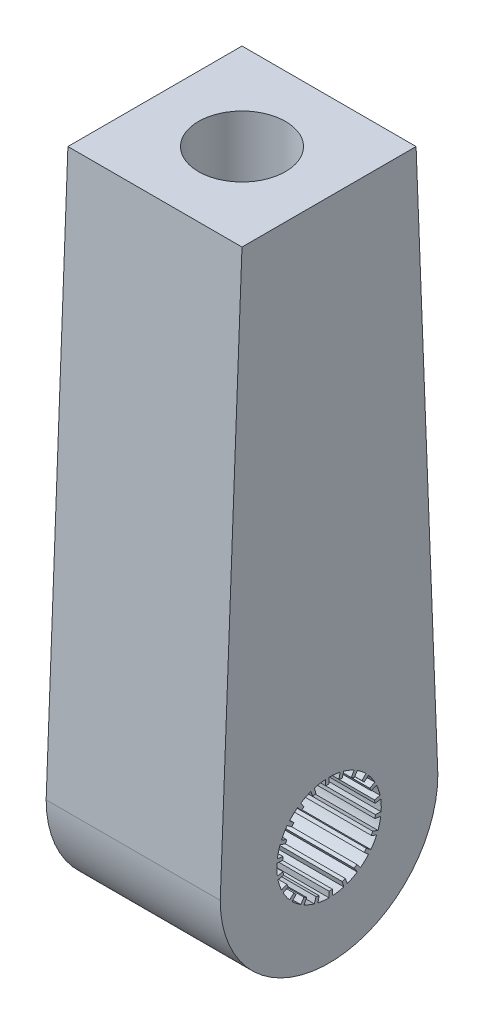
SolidWorks part; units mm, degrees
ref_plane "Front Plane" through (0, 0, 0) normal (0, 0, 1) x (1, 0, 0)
ref_plane "Top Plane" through (0, 0, 0) normal (0, 1, 0) x (1, 0, 0)
ref_plane "Right Plane" through (0, 0, 0) normal (1, 0, 0) x (0, 0, -1)
sketch "Sketch1" plane through (0, 0, 0) normal (1, 0, 0) x (0, 0, -1)
  line L1 (0, 63.75) -> (10, 63.75)
  line L2 (10, 63.75) -> (12.5, 0)
  line L4 (-12.5, 0) -> (-10, 63.75)
  line L5 (-10, 63.75) -> (0, 63.75)
  circle A0 centre (0, 0) radius 6
  arc A2 (-12.4616, 0.9789) -> (12.4616, 0.9789) centre (0, 0) ccw
  dimension "D1" = 12
  dimension "D3" = 25
  dimension "D4" = 63.75
  dimension "D5" = 10
  dimension "D6" = 10
extrude "Boss-Extrude1" add sketch "Sketch1" along normal blind 20 contours A2 A0
sketch "Sketch2" plane through (0, 63.75, 0) normal (0, 1, 0) x (1, 0, 0)
  line L0 (0, -10) -> (0, 10) construction
  circle A0 centre (10, 0) radius 5
  dimension "D2" = 10
  dimension "D1" = 10
extrude "Cut-Extrude1" cut sketch "Sketch2" against normal blind 50
sketch "Sketch3" plane through (20, 0, 0) normal (1, 0, 0) x (0, 0, -1)
  line L0 (-0.0029, 6.4021) -> (-0.0028, 6)
  line L1 (1.5045, 5.1237) -> (1.6904, 5.757)
  line L2 (1.6904, 5.757) -> (1.8037, 6.1428)
  line L3 (2.5593, 4.6868) -> (2.8756, 5.266)
  line L4 (1.1352, 5.2179) -> (1.2755, 5.8629)
  line L5 (2.887, 4.4923) -> (3.2438, 5.0475)
  line L6 (3.2438, 5.0475) -> (3.4612, 5.3858)
  line L7 (1.8009, 6.1436) -> (1.6877, 5.7577)
  line L8 (3.776, 3.7759) -> (4.2427, 4.2426)
  line L9 (4.0357, 3.497) -> (4.5345, 3.9292)
  line L10 (4.5345, 3.9292) -> (4.8384, 4.1925)
  line L11 (3.4588, 5.3874) -> (3.2415, 5.049)
  line L12 (4.6868, 2.5591) -> (5.2661, 2.8754)
  line L13 (4.8574, 2.2183) -> (5.4578, 2.4925)
  line L14 (5.4578, 2.4925) -> (5.8236, 2.6595)
  line L15 (4.8365, 4.1947) -> (4.5327, 3.9313)
  line L16 (5.218, 1.135) -> (5.8629, 1.2753)
  line L17 (5.2856, 0.76) -> (5.9389, 0.8539)
  line L18 (5.9389, 0.8539) -> (6.337, 0.9111)
  line L19 (5.8223, 2.6622) -> (5.4566, 2.495)
  line L20 (5.3264, -0.381) -> (5.9847, -0.4281)
  line L21 (5.2856, -0.76) -> (5.9389, -0.8539)
  line L22 (5.9389, -0.8539) -> (6.337, -0.9111)
  line L23 (6.3365, 0.914) -> (5.9385, 0.8566)
  line L24 (5.0033, -1.8662) -> (5.6217, -2.0969)
  line L25 (4.8574, -2.2183) -> (5.4578, -2.4925)
  line L26 (5.4578, -2.4925) -> (5.8236, -2.6595)
  line L27 (6.3374, -0.9082) -> (5.9393, -0.8512)
  line L28 (4.2748, -3.2002) -> (4.8032, -3.5957)
  line L29 (4.0357, -3.497) -> (4.5345, -3.9292)
  line L30 (4.5345, -3.9292) -> (4.8384, -4.1925)
  line L31 (5.8248, -2.6569) -> (5.4589, -2.49)
  line L32 (3.2001, -4.2749) -> (3.5956, -4.8033)
  line L33 (2.887, -4.4923) -> (3.2438, -5.0475)
  line L34 (3.2438, -5.0475) -> (3.4612, -5.3858)
  line L35 (4.8403, -4.1903) -> (4.5363, -3.9271)
  line L36 (1.8661, -5.0033) -> (2.0967, -5.6217)
  line L37 (1.5045, -5.1237) -> (1.6904, -5.757)
  line L38 (1.6904, -5.757) -> (1.8037, -6.1428)
  line L39 (3.4637, -5.3842) -> (3.2462, -5.046)
  line L40 (0.3809, -5.3264) -> (0.4279, -5.9847)
  line L41 (0, -5.34) -> (0, -6)
  line L42 (0, -6) -> (0, -6.4021)
  line L43 (1.8065, -6.142) -> (1.693, -5.7562)
  line L44 (-1.1352, -5.2179) -> (-1.2755, -5.8629)
  line L45 (-1.5045, -5.1237) -> (-1.6904, -5.757)
  line L46 (-1.6904, -5.757) -> (-1.8037, -6.1428)
  line L47 (0.0029, -6.4021) -> (0.0028, -6)
  line L48 (-2.5593, -4.6868) -> (-2.8756, -5.266)
  line L49 (-2.887, -4.4923) -> (-3.2438, -5.0475)
  line L50 (-3.2438, -5.0475) -> (-3.4612, -5.3858)
  line L51 (-1.8009, -6.1436) -> (-1.6877, -5.7577)
  line L52 (-3.776, -3.7759) -> (-4.2427, -4.2426)
  line L53 (-4.0357, -3.497) -> (-4.5345, -3.9292)
  line L54 (-4.5345, -3.9292) -> (-4.8384, -4.1925)
  line L55 (-3.4588, -5.3874) -> (-3.2415, -5.049)
  line L56 (-4.6868, -2.5591) -> (-5.2661, -2.8754)
  line L57 (-4.8574, -2.2183) -> (-5.4578, -2.4925)
  line L58 (-5.4578, -2.4925) -> (-5.8236, -2.6595)
  line L59 (-4.8365, -4.1947) -> (-4.5327, -3.9313)
  line L60 (-5.218, -1.135) -> (-5.8629, -1.2753)
  line L61 (-5.2856, -0.76) -> (-5.9389, -0.8539)
  line L62 (-5.9389, -0.8539) -> (-6.337, -0.9111)
  line L63 (-5.8223, -2.6622) -> (-5.4566, -2.495)
  line L64 (-5.3264, 0.381) -> (-5.9847, 0.4281)
  line L65 (-5.2856, 0.76) -> (-5.9389, 0.8539)
  line L66 (-5.9389, 0.8539) -> (-6.337, 0.9111)
  line L67 (-6.3365, -0.914) -> (-5.9385, -0.8566)
  line L68 (-5.0033, 1.8662) -> (-5.6217, 2.0969)
  line L69 (-4.8574, 2.2183) -> (-5.4578, 2.4925)
  line L70 (-5.4578, 2.4925) -> (-5.8236, 2.6595)
  line L71 (-6.3374, 0.9082) -> (-5.9393, 0.8512)
  line L72 (-4.2748, 3.2002) -> (-4.8032, 3.5957)
  line L73 (-4.0357, 3.497) -> (-4.5345, 3.9292)
  line L74 (-4.5345, 3.9292) -> (-4.8384, 4.1925)
  line L75 (-5.8248, 2.6569) -> (-5.4589, 2.49)
  line L76 (-3.2001, 4.2749) -> (-3.5956, 4.8033)
  line L77 (-2.887, 4.4923) -> (-3.2438, 5.0475)
  line L78 (-3.2438, 5.0475) -> (-3.4612, 5.3858)
  line L79 (-4.8403, 4.1903) -> (-4.5363, 3.9271)
  line L80 (-1.8661, 5.0033) -> (-2.0967, 5.6217)
  line L81 (-1.5045, 5.1237) -> (-1.6904, 5.757)
  line L82 (-1.6904, 5.757) -> (-1.8037, 6.1428)
  line L83 (-3.4637, 5.3842) -> (-3.2462, 5.046)
  line L84 (-0.3809, 5.3264) -> (-0.4279, 5.9847)
  line L85 (0, 5.34) -> (0, 6)
  line L86 (0, 6) -> (0, 6.4021)
  line L87 (-1.8065, 6.142) -> (-1.693, 5.7562)
  arc A2 (1.3548, 5.8451) -> (1.2755, 5.8629) centre (0, 0) ccw
  arc A3 (1.5045, 5.1237) -> (1.1352, 5.2179) centre (0, 0) ccw
  arc A4 (1.6904, 5.757) -> (1.2755, 5.8629) centre (0, 0) ccw
  arc A6 (-0.0028, 6) -> (1.2755, 5.8629) centre (0, 0) cw
  arc A7 (-0.0029, 6.4021) -> (1.8037, 6.1428) centre (0, 0) cw
  arc A8 (2.887, 4.4923) -> (2.5593, 4.6868) centre (0, 0) ccw
  arc A9 (1.8009, 6.1436) -> (3.4612, 5.3858) centre (0, 0) cw
  arc A10 (1.6877, 5.7577) -> (2.8756, 5.266) centre (0, 0) cw
  arc A11 (4.0357, 3.497) -> (3.776, 3.7759) centre (0, 0) ccw
  arc A12 (3.4588, 5.3874) -> (4.8384, 4.1925) centre (0, 0) cw
  arc A13 (3.2415, 5.049) -> (4.2427, 4.2426) centre (0, 0) cw
  arc A14 (4.8574, 2.2183) -> (4.6868, 2.5591) centre (0, 0) ccw
  arc A15 (4.8365, 4.1947) -> (5.8236, 2.6595) centre (0, 0) cw
  arc A16 (4.5327, 3.9313) -> (5.2661, 2.8754) centre (0, 0) cw
  arc A17 (5.2856, 0.76) -> (5.218, 1.135) centre (0, 0) ccw
  arc A18 (5.8223, 2.6622) -> (6.337, 0.9111) centre (0, 0) cw
  arc A19 (5.4566, 2.495) -> (5.8629, 1.2753) centre (0, 0) cw
  arc A20 (5.2856, -0.76) -> (5.3264, -0.381) centre (0, 0) ccw
  arc A21 (6.3365, 0.914) -> (6.337, -0.9111) centre (0, 0) cw
  arc A22 (5.9385, 0.8566) -> (5.9847, -0.4281) centre (0, 0) cw
  arc A23 (4.8574, -2.2183) -> (5.0033, -1.8662) centre (0, 0) ccw
  arc A24 (6.3374, -0.9082) -> (5.8236, -2.6595) centre (0, 0) cw
  arc A25 (5.9393, -0.8512) -> (5.6217, -2.0969) centre (0, 0) cw
  arc A26 (4.0357, -3.497) -> (4.2748, -3.2002) centre (0, 0) ccw
  arc A27 (5.8248, -2.6569) -> (4.8384, -4.1925) centre (0, 0) cw
  arc A28 (5.4589, -2.49) -> (4.8032, -3.5957) centre (0, 0) cw
  arc A29 (2.887, -4.4923) -> (3.2001, -4.2749) centre (0, 0) ccw
  arc A30 (4.8403, -4.1903) -> (3.4612, -5.3858) centre (0, 0) cw
  arc A31 (4.5363, -3.9271) -> (3.5956, -4.8033) centre (0, 0) cw
  arc A32 (1.5045, -5.1237) -> (1.8661, -5.0033) centre (0, 0) ccw
  arc A33 (3.4637, -5.3842) -> (1.8037, -6.1428) centre (0, 0) cw
  arc A34 (3.2462, -5.046) -> (2.0967, -5.6217) centre (0, 0) cw
  arc A35 (0, -5.34) -> (0.3809, -5.3264) centre (0, 0) ccw
  arc A36 (1.8065, -6.142) -> (0, -6.4021) centre (0, 0) cw
  arc A37 (1.693, -5.7562) -> (0.4279, -5.9847) centre (0, 0) cw
  arc A38 (-1.5045, -5.1237) -> (-1.1352, -5.2179) centre (0, 0) ccw
  arc A39 (0.0029, -6.4021) -> (-1.8037, -6.1428) centre (0, 0) cw
  arc A40 (0.0028, -6) -> (-1.2755, -5.8629) centre (0, 0) cw
  arc A41 (-2.887, -4.4923) -> (-2.5593, -4.6868) centre (0, 0) ccw
  arc A42 (-1.8009, -6.1436) -> (-3.4612, -5.3858) centre (0, 0) cw
  arc A43 (-1.6877, -5.7577) -> (-2.8756, -5.266) centre (0, 0) cw
  arc A44 (-4.0357, -3.497) -> (-3.776, -3.7759) centre (0, 0) ccw
  arc A45 (-3.4588, -5.3874) -> (-4.8384, -4.1925) centre (0, 0) cw
  arc A46 (-3.2415, -5.049) -> (-4.2427, -4.2426) centre (0, 0) cw
  arc A47 (-4.8574, -2.2183) -> (-4.6868, -2.5591) centre (0, 0) ccw
  arc A48 (-4.8365, -4.1947) -> (-5.8236, -2.6595) centre (0, 0) cw
  arc A49 (-4.5327, -3.9313) -> (-5.2661, -2.8754) centre (0, 0) cw
  arc A50 (-5.2856, -0.76) -> (-5.218, -1.135) centre (0, 0) ccw
  arc A51 (-5.8223, -2.6622) -> (-6.337, -0.9111) centre (0, 0) cw
  arc A52 (-5.4566, -2.495) -> (-5.8629, -1.2753) centre (0, 0) cw
  arc A53 (-5.2856, 0.76) -> (-5.3264, 0.381) centre (0, 0) ccw
  arc A54 (-6.3365, -0.914) -> (-6.337, 0.9111) centre (0, 0) cw
  arc A55 (-5.9385, -0.8566) -> (-5.9847, 0.4281) centre (0, 0) cw
  arc A56 (-4.8574, 2.2183) -> (-5.0033, 1.8662) centre (0, 0) ccw
  arc A57 (-6.3374, 0.9082) -> (-5.8236, 2.6595) centre (0, 0) cw
  arc A58 (-5.9393, 0.8512) -> (-5.6217, 2.0969) centre (0, 0) cw
  arc A59 (-4.0357, 3.497) -> (-4.2748, 3.2002) centre (0, 0) ccw
  arc A60 (-5.8248, 2.6569) -> (-4.8384, 4.1925) centre (0, 0) cw
  arc A61 (-5.4589, 2.49) -> (-4.8032, 3.5957) centre (0, 0) cw
  arc A62 (-2.887, 4.4923) -> (-3.2001, 4.2749) centre (0, 0) ccw
  arc A63 (-4.8403, 4.1903) -> (-3.4612, 5.3858) centre (0, 0) cw
  arc A64 (-4.5363, 3.9271) -> (-3.5956, 4.8033) centre (0, 0) cw
  arc A65 (-1.5045, 5.1237) -> (-1.8661, 5.0033) centre (0, 0) ccw
  arc A66 (-3.4637, 5.3842) -> (-1.8037, 6.1428) centre (0, 0) cw
  arc A67 (-3.2462, 5.046) -> (-2.0967, 5.6217) centre (0, 0) cw
  arc A68 (0, 5.34) -> (-0.3809, 5.3264) centre (0, 0) ccw
  arc A69 (-1.8065, 6.142) -> (0, 6.4021) centre (0, 0) cw
  arc A70 (-1.693, 5.7562) -> (-0.4279, 5.9847) centre (0, 0) cw
  circle M6 centre (0, 0) radius 6
  dimension "D1" = 16.39
  dimension "D3" = 4.09
  dimension "D2" = 22
extrude "Boss-Extrude2" add sketch "Sketch3" against normal blind 20 contours A3 L1 L4 M6 | A68 L85 L84 M6 | A65 L81 L80 M6 | A8 L5 L3 M6 | A11 L9 L8 M6 | A14 L13 L12 M6 | A17 L17 L16 M6 | A20 L21 L20 M6 | A23 L25 L24 M6 | A26 L29 L28 M6 | A29 L33 L32 M6 | A35 L41 L40 M6 | A38 L45 L44 M6 | A44 L53 L52 M6 | A47 L57 L56 M6 | A53 L65 L64 M6 | A56 L69 L68 M6 | A59 L73 L72 M6 | A62 L77 L76 M6 | A66 L78 L87 M6 | A63 L74 L83 M6 | A60 L70 L79 M6 | A57 L66 L75 M6 | A54 L62 L71 M6 | A48 L54 L63 M6 | A45 L50 L59 M6 | A42 L46 L55 M6 | A36 L38 L47 M6 | A30 L30 L39 M6 | A27 L26 L35 M6 | A24 L22 L31 M6 | A21 L18 L27 M6 | A18 L14 L23 M6 | A15 L10 L19 M6 | A12 L6 L15 M6 | A9 L2 L11 M6 | A69 L82 L0 M6 | A7 L86 L7 M6 | A32 L37 L36 M6 | A41 L49 L48 M6
